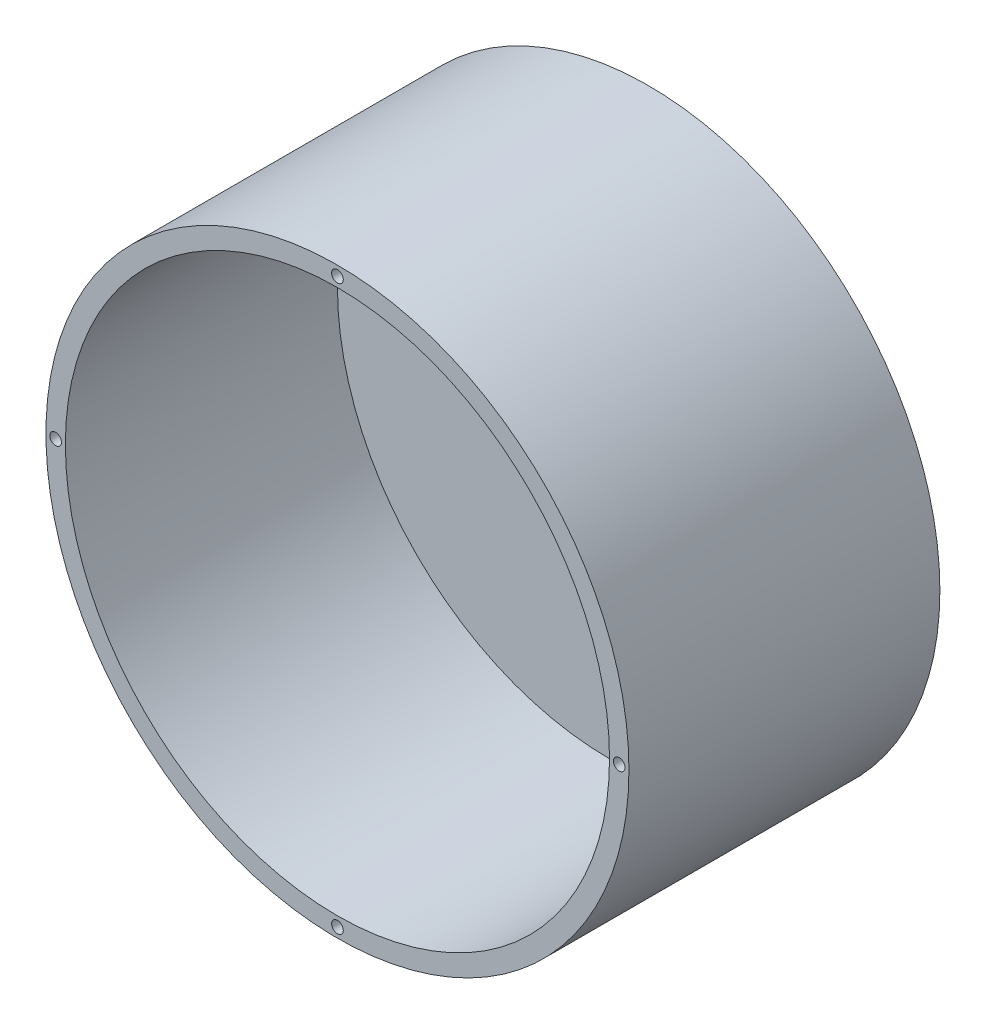
SolidWorks part; units mm, degrees
ref_plane "Front Plane" through (0, 0, 0) normal (0, 0, 1) x (1, 0, 0)
ref_plane "Top Plane" through (0, 0, 0) normal (0, 1, 0) x (1, 0, 0)
ref_plane "Right Plane" through (0, 0, 0) normal (1, 0, 0) x (0, 0, -1)
sketch "Sketch1" plane through (0, 0, 0) normal (0, 0, 1) x (1, 0, 0)
  circle A0 centre (0, 0) radius 35
  circle A1 centre (0, 0) radius 37.5
  dimension "D1" = 70
  dimension "D2" = 75
extrude "Boss-Extrude1" add sketch "Sketch1" along normal blind 40 contours A0 | A1
sketch "Sketch2" plane through (0, 0, 0) normal (0, 0, -1) x (-1, 0, 0)
  circle A0 centre (0, 0) radius 35
extrude "Boss-Extrude2" add sketch "Sketch2" against normal blind 5
sketch "Sketch3" plane through (0, 0, 40) normal (0, 0, 1) x (1, 0, 0)
  circle A0 centre (0, 36.25) radius 0.75
  circle A1 centre (0, 0) radius 35 construction
  circle A2 centre (36.25, 0) radius 0.75
  circle A3 centre (0, -36.25) radius 0.75
  circle A4 centre (-36.25, 0) radius 0.75
  point P13 (0, 0)
  dimension "D1" = 1.5
  dimension "D2" = 4
  dimension "36.75" = 36.25
extrude "Cut-Extrude1" cut sketch "Sketch3" against normal blind 5
